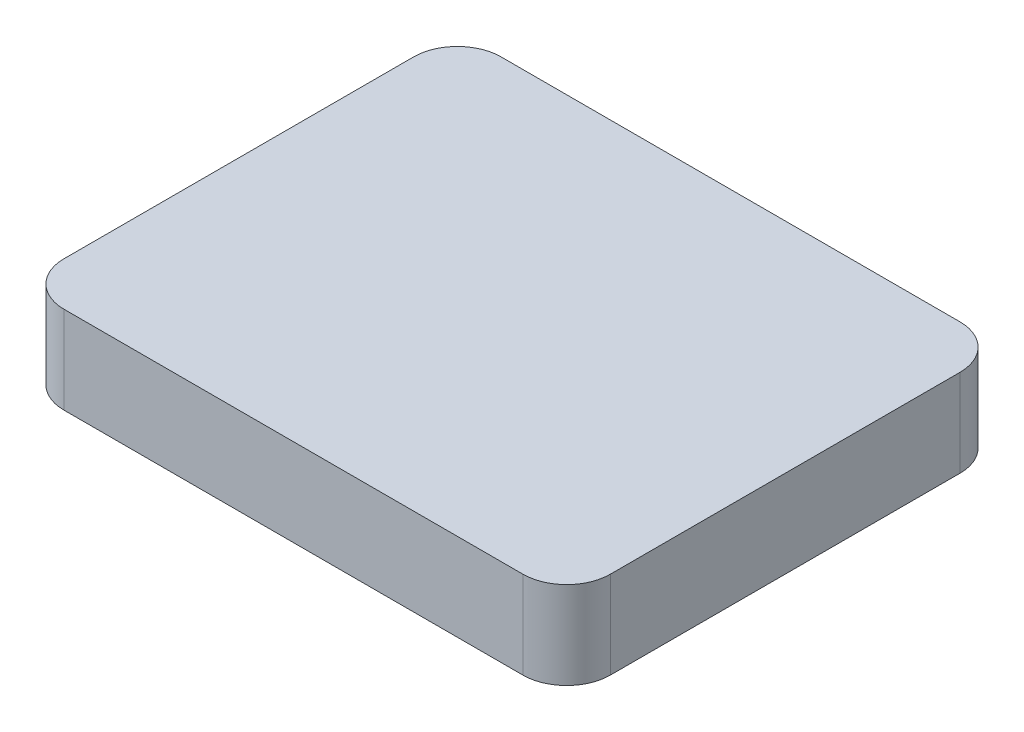
SolidWorks part; units mm, degrees
ref_plane "Front Plane" through (0, 0, 0) normal (0, 0, 1) x (1, 0, 0)
ref_plane "Top Plane" through (0, 0, 0) normal (0, 1, 0) x (1, 0, 0)
ref_plane "Right Plane" through (0, 0, 0) normal (1, 0, 0) x (0, 0, -1)
sketch "Sketch1" plane through (0, 0, 0) normal (0, 1, 0) x (1, 0, 0)
  line L1 (-125, 100) -> (125, 100)
  line L2 (-125, 100) -> (-125, -100)
  line L3 (-125, -100) -> (125, -100)
  line L4 (125, 100) -> (125, -100)
  line L5 (-125, 100) -> (125, -100) construction
  line L6 (-125, -100) -> (125, 100) construction
  point P0 (0, 0)
  dimension "D1" = 250
  dimension "D2" = 200
extrude "Boss-Extrude1" add sketch "Sketch1" along normal blind 40
fillet "Fillet1" radius 20 4 edges at (-125, 20, 100) (-125, 20, -100) (125, 20, -100) (125, 20, 100)
